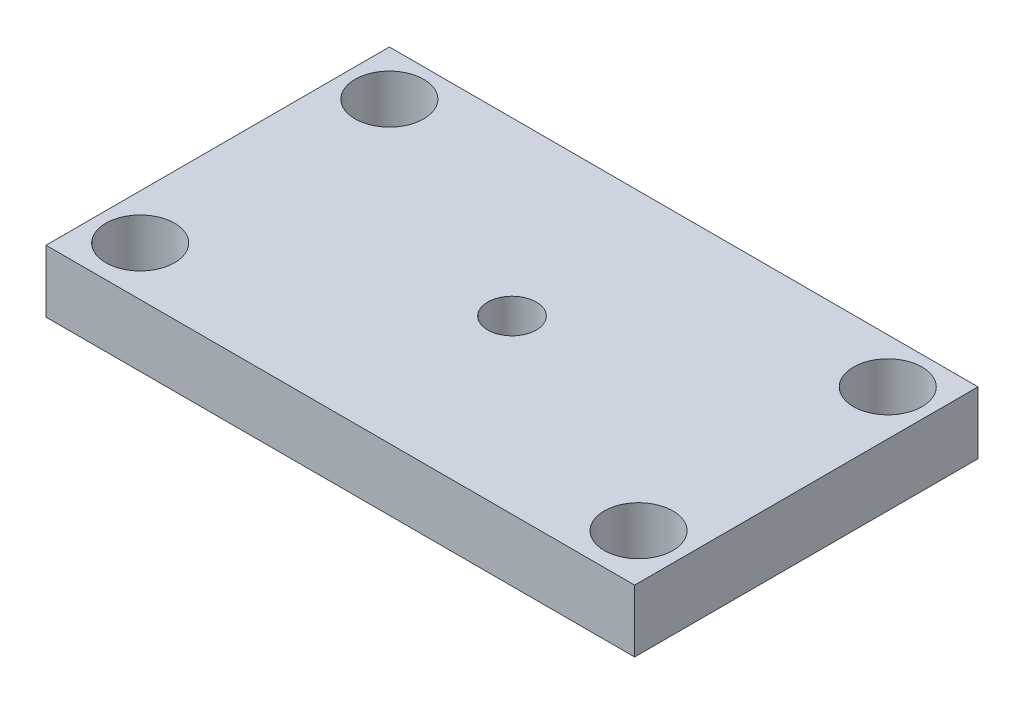
SolidWorks part; units mm, degrees
ref_plane "Front Plane" through (0, 0, 0) normal (0, 0, 1) x (1, 0, 0)
ref_plane "Top Plane" through (0, 0, 0) normal (0, 1, 0) x (1, 0, 0)
ref_plane "Right Plane" through (0, 0, 0) normal (1, 0, 0) x (0, 0, -1)
sketch "Sketch1" plane through (0, 0, 0) normal (0, 1, 0) x (1, 0, 0)
  line L0 (4.6, 30.4) -> (0, 30.4) construction
  line L1 (0, 0) -> (60, 0)
  line L2 (0, 0) -> (0, 35)
  line L3 (0, 35) -> (60, 35)
  line L4 (60, 0) -> (60, 35)
  line L5 (4.6, 30.4) -> (55.4, 30.4) construction
  line L6 (4.6, 30.4) -> (4.6, 5) construction
  line L7 (4.6, 5) -> (55.4, 5) construction
  line L8 (55.4, 30.4) -> (55.4, 5) construction
  line L9 (4.6, 30.4) -> (4.6, 35) construction
  circle A0 centre (4.6, 30.4) radius 3.5
  circle A1 centre (55.4, 30.4) radius 3.5
  circle A2 centre (4.6, 5) radius 3.5
  circle A3 centre (55.4, 5) radius 3.5
  circle A4 centre (30, 17.5) radius 2.475
  point P13 (30, 30.4)
  point P14 (30, 35)
  point P20 (60, 17.5)
  dimension "D5" = 7
  dimension "D6" = 4.95
  dimension "D1" = 60
  dimension "D2" = 35
  dimension "D3" = 50.8
  dimension "D4" = 25.4
extrude "Boss-Extrude1" add sketch "Sketch1" along normal blind 6.35
